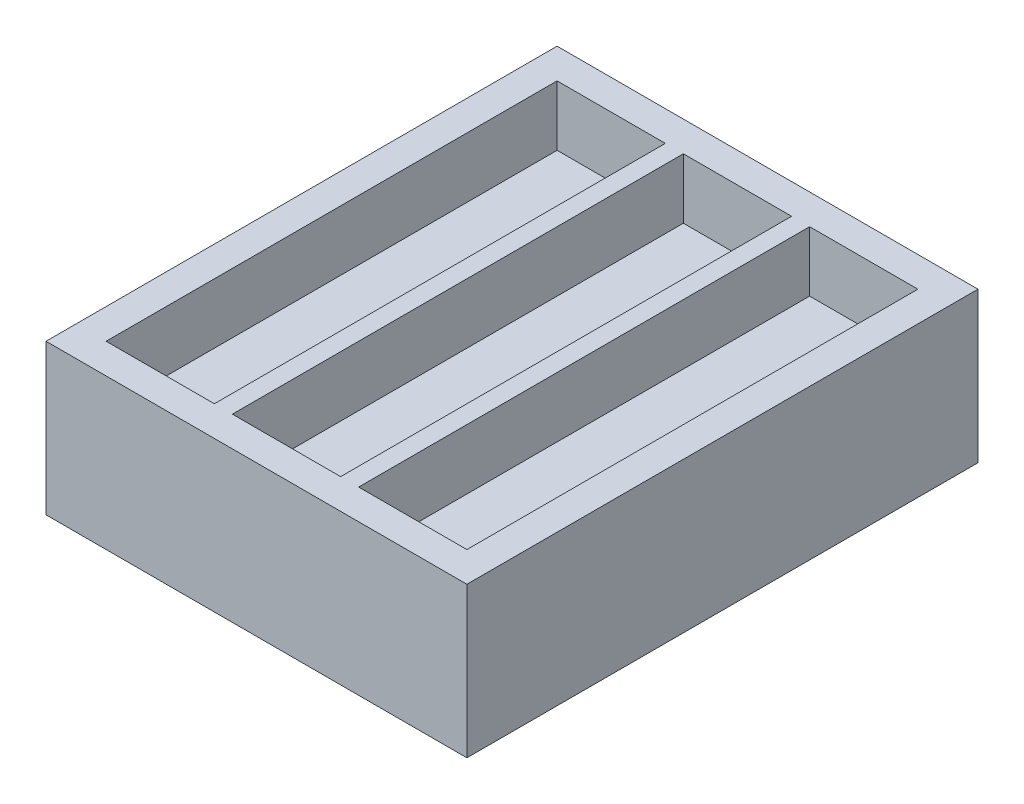
SolidWorks part; units mm, degrees
ref_plane "Front Plane" through (0, 0, 0) normal (0, 0, 1) x (1, 0, 0)
ref_plane "Top Plane" through (0, 0, 0) normal (0, 1, 0) x (1, 0, 0)
ref_plane "Right Plane" through (0, 0, 0) normal (1, 0, 0) x (0, 0, -1)
sketch "Sketch1" plane through (0, 0, 0) normal (0, 1, 0) x (1, 0, 0)
  line L1 (-35, -42.5) -> (35, -42.5)
  line L2 (-35, -42.5) -> (-35, 42.5)
  line L3 (-35, 42.5) -> (35, 42.5)
  line L4 (35, -42.5) -> (35, 42.5)
  line L5 (-35, -42.5) -> (35, 42.5) construction
  line L6 (-35, 42.5) -> (35, -42.5) construction
  point P0 (0, 0)
  dimension "D1" = 85
  dimension "D2" = 70
extrude "Boss-Extrude1" add sketch "Sketch1" along normal blind 25
sketch "Sketch2" plane through (0, 25, 0) normal (0, 1, 0) x (1, 0, 0)
  line L0 (-35, 42.5) -> (-35, -42.5) construction
  line L1 (-30, 37.5) -> (-12, 37.5)
  line L2 (-30, 37.5) -> (-30, -37.5)
  line L3 (-30, -37.5) -> (-12, -37.5)
  line L4 (-12, 37.5) -> (-12, -37.5)
  line L5 (-30, 37.5) -> (-12, -37.5) construction
  line L6 (-30, -37.5) -> (-12, 37.5) construction
  line L7 (35, 42.5) -> (-35, 42.5) construction
  line L8 (-9, 37.5) -> (-9, -37.5)
  line L9 (-9, 37.5) -> (9, 37.5)
  line L10 (9, 37.5) -> (9, -37.5)
  line L11 (-9, -37.5) -> (9, -37.5)
  line L12 (12, 37.5) -> (12, -37.5)
  line L13 (12, 37.5) -> (30, 37.5)
  line L14 (30, 37.5) -> (30, -37.5)
  line L15 (12, -37.5) -> (30, -37.5)
  line L16 (35, -42.5) -> (35, 42.5) construction
  point P4 (-21, 0)
  dimension "D1" = 18
  dimension "D2" = 5
  dimension "D3" = 75
  dimension "D4" = 5
  dimension "D6" = 5
  dimension "D5" = 3
extrude "Cut-Extrude1" cut sketch "Sketch2" against normal blind 10
